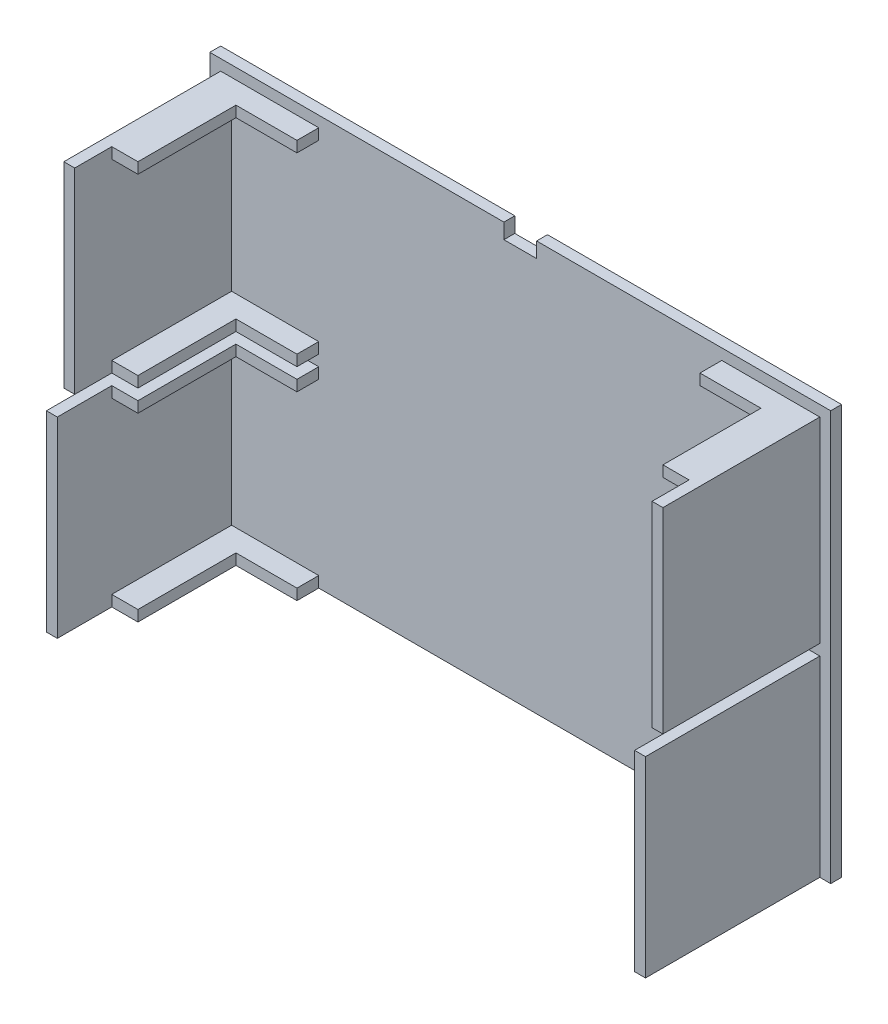
SolidWorks part; units mm, degrees
ref_plane "Front Plane" through (0, 0, 0) normal (0, 0, 1) x (1, 0, 0)
ref_plane "Top Plane" through (0, 0, 0) normal (0, 1, 0) x (1, 0, 0)
ref_plane "Right Plane" through (0, 0, 0) normal (1, 0, 0) x (0, 0, -1)
sketch "Sketch1" plane through (0, 0, 0) normal (0, 0, 1) x (1, 0, 0)
  line L1 (-138.7659, 75.117) -> (146.2341, 75.117)
  line L2 (-138.7659, 75.117) -> (-138.7659, -112.883)
  line L3 (-138.7659, -112.883) -> (146.2341, -112.883)
  line L4 (146.2341, 75.117) -> (146.2341, -112.883)
  dimension "D1" = 285
  dimension "D2" = 188
extrude "Boss-Extrude1" add sketch "Sketch1" along normal blind 5
sketch "Sketch2" plane through (0, -112.883, 0) normal (0, -1, 0) x (1, 0, 0)
  line L0 (-138.7659, 5) -> (146.2341, 5) construction
  line L1 (-3.7659, 5) -> (11.2341, 5)
  line L2 (-3.7659, 5) -> (-3.7659, 0)
  line L3 (-3.7659, 0) -> (11.2341, 0)
  line L4 (11.2341, 5) -> (11.2341, 0)
  line L5 (-138.7659, 0) -> (146.2341, 0) construction
  line L6 (-138.7659, 5) -> (-138.7659, 0) construction
  line L7 (146.2341, 5) -> (146.2341, 0) construction
  dimension "D1" = 15
  dimension "D2" = 135
  dimension "D3" = 135
sketch "Sketch3" plane through (0, 0, 5) normal (0, 0, 1) x (1, 0, 0)
  line L0 (146.2341, 75.117) -> (-138.7659, 75.117) construction
  line L1 (-133.7659, 70.117) -> (-128.7659, 70.117)
  line L2 (-133.7659, 70.117) -> (-133.7659, -19.883)
  line L3 (-133.7659, -19.883) -> (-128.7659, -19.883)
  line L4 (-128.7659, 70.117) -> (-128.7659, -19.883)
  line L5 (-138.7659, 75.117) -> (-138.7659, -112.883) construction
  dimension "D1" = 5
  dimension "D2" = 90
  dimension "D3" = 5
  dimension "D4" = 5
extrude "Boss-Extrude2" add sketch "Sketch3" along normal blind 72
sketch "Sketch6" plane through (0, 0, 5) normal (0, 0, 1) x (1, 0, 0)
  line L0 (-128.7659, 70.117) -> (-88.7659, 70.117)
  line L1 (-88.7659, 70.117) -> (-88.7659, 65.117)
  line L2 (-88.7659, 65.117) -> (-128.7659, 65.117)
  line L3 (-128.7659, -19.883) -> (-128.7659, 70.117) construction
  line L4 (-128.7659, 70.117) -> (-128.7659, 65.117)
  dimension "D1" = 40
  dimension "D2" = 5
  dimension "D3" = 40
extrude "Boss-Extrude3" add sketch "Sketch6" along normal blind 10
sketch "Sketch7" plane through (0, 0, 15) normal (0, 0, 1) x (1, 0, 0)
  line L0 (-128.7659, 70.117) -> (-116.7659, 70.117)
  line L1 (-88.7659, 70.117) -> (-133.7659, 70.117) construction
  line L2 (-116.7659, 70.117) -> (-116.7659, 65.117)
  line L3 (-128.7659, 65.117) -> (-88.7659, 65.117) construction
  line L4 (-116.7659, 65.117) -> (-128.7659, 65.117)
  line L5 (-128.7659, 65.117) -> (-88.7659, 65.117) construction
  line L6 (-128.7659, 65.117) -> (-128.7659, 70.117)
  dimension "D1" = 12
extrude "Boss-Extrude4" add sketch "Sketch7" along normal blind 45
sketch "Sketch8" plane through (0, 0, 77) normal (0, 0, 1) x (1, 0, 0)
  line L0 (-128.7659, -19.883) -> (-128.7659, 70.117) construction
  line L1 (-128.7659, -19.883) -> (-88.7659, -19.883)
  line L2 (-128.7659, -19.883) -> (-128.7659, -14.883)
  line L3 (-128.7659, -14.883) -> (-88.7659, -14.883)
  line L4 (-88.7659, -19.883) -> (-88.7659, -14.883)
  line L5 (-128.7659, -19.883) -> (-128.7659, 65.117) construction
  dimension "D1" = 5
  dimension "D2" = 40
extrude "Boss-Extrude5" add sketch "Sketch8" against normal blind 72
sketch "Sketch9" plane through (0, -19.883, 0) normal (0, -1, 0) x (1, 0, 0)
  line L0 (-116.7659, 15) -> (-88.7659, 15)
  line L1 (-88.7659, 5) -> (-88.7659, 77) construction
  line L2 (-88.7659, 15) -> (-88.7659, 77)
  line L3 (-88.7659, 77) -> (-128.7659, 77)
  line L4 (-128.7659, 77) -> (-128.7659, 60)
  line L5 (-128.7659, 60) -> (-116.7659, 60)
  line L6 (-116.7659, 60) -> (-116.7659, 15)
extrude "Cut-Extrude4" cut sketch "Sketch9" along normal through all both and the other way through all
sketch "Sketch11" plane through (0, 0, 5) normal (0, 0, 1) x (1, 0, 0)
  line L0 (3.7341, 75.117) -> (3.7341, -112.883) construction
  line L1 (146.2341, 75.117) -> (-138.7659, 75.117) construction
  line L2 (-138.7659, -112.883) -> (146.2341, -112.883) construction
sketch "Sketch13" plane through (0, 0, 5) normal (0, 0, 1) x (1, 0, 0)
  line L0 (146.2341, 75.117) -> (-138.7659, 75.117) construction
  line L1 (136.2341, 70.117) -> (141.2341, 70.117)
  line L2 (136.2341, 70.117) -> (136.2341, -19.883)
  line L3 (136.2341, -19.883) -> (141.2341, -19.883)
  line L4 (141.2341, 70.117) -> (141.2341, -19.883)
  line L5 (-128.7659, 70.117) -> (-133.7659, 70.117) construction
  line L8 (146.2341, -112.883) -> (146.2341, 75.117) construction
  dimension "D1" = 5
  dimension "D2" = 5
  dimension "D3" = 90
  dimension "D4" = 5
  dimension "D5" = 5
extrude "Boss-Extrude6" add sketch "Sketch13" along normal blind 72
sketch "Sketch14" plane through (0, 0, 5) normal (0, 0, 1) x (1, 0, 0)
  line L1 (136.2341, 70.117) -> (96.2341, 70.117)
  line L2 (136.2341, 70.117) -> (136.2341, 65.117)
  line L3 (136.2341, 65.117) -> (96.2341, 65.117)
  line L4 (96.2341, 70.117) -> (96.2341, 65.117)
  dimension "D1" = 40
  dimension "D2" = 5
extrude "Boss-Extrude7" add sketch "Sketch14" along normal blind 55
sketch "Sketch15" plane through (0, 65.117, 0) normal (0, -1, 0) x (1, 0, 0)
sketch "Sketch16" plane through (0, 65.117, 0) normal (0, -1, 0) x (1, 0, 0)
  line L1 (96.2341, 60) -> (124.2341, 60)
  line L2 (96.2341, 60) -> (96.2341, 15)
  line L3 (96.2341, 15) -> (124.2341, 15)
  line L4 (124.2341, 60) -> (124.2341, 15)
  dimension "D1" = 28
  dimension "D2" = 45
extrude "Cut-Extrude5" cut sketch "Sketch16" against normal through all both and the other way through all
sketch "Sketch17" plane through (0, 0, 0) normal (0, 0, 1) x (1, 0, 0)
  line L1 (136.2341, -19.883) -> (96.2341, -19.883)
  line L2 (136.2341, -19.883) -> (136.2341, -14.883)
  line L3 (136.2341, -14.883) -> (96.2341, -14.883)
  line L4 (96.2341, -19.883) -> (96.2341, -14.883)
  dimension "D1" = 40
  dimension "D2" = 5
extrude "Boss-Extrude9" add sketch "Sketch17" along normal blind 55
sketch "Sketch21" plane through (0, -14.883, 0) normal (0, 1, 0) x (1, 0, 0)
  line L0 (136.2341, -55) -> (96.2341, -55) construction
  line L1 (96.2341, -15) -> (123.996, -15)
  line L2 (96.2341, -15) -> (96.2341, -55)
  line L3 (96.2341, -55) -> (123.996, -55)
  line L4 (123.996, -15) -> (123.996, -55)
extrude "Cut-Extrude6" cut sketch "Sketch21" against normal through all both and the other way through all
sketch "Sketch22" plane through (0, 0, 5) normal (0, 0, 1) x (1, 0, 0)
  line L0 (-138.7659, -112.883) -> (146.2341, -112.883) construction
  line L1 (-133.7659, -24.883) -> (-128.7659, -24.883)
  line L2 (-133.7659, -24.883) -> (-133.7659, -112.883)
  line L3 (-133.7659, -112.883) -> (-128.7659, -112.883)
  line L4 (-128.7659, -24.883) -> (-128.7659, -112.883)
  line L6 (-133.7659, -19.883) -> (-128.7659, -19.883) construction
  line L7 (-138.7659, 75.117) -> (-138.7659, -112.883) construction
  line L8 (-133.7659, 70.117) -> (-133.7659, -19.883) construction
  dimension "D1" = 5
  dimension "D2" = 5
  dimension "D3" = 5
  dimension "D4" = 5
  dimension "D5" = 5
extrude "Boss-Extrude10" add sketch "Sketch22" along normal blind 80
sketch "Sketch23" plane through (0, 0, 5) normal (0, 0, 1) x (1, 0, 0)
  line L0 (-128.7659, -112.883) -> (-128.7659, -24.883) construction
  line L1 (-128.7659, -107.883) -> (-88.7659, -107.883)
  line L2 (-128.7659, -107.883) -> (-128.7659, -112.883)
  line L3 (-128.7659, -112.883) -> (-88.7659, -112.883)
  line L4 (-88.7659, -107.883) -> (-88.7659, -112.883)
  line L5 (-128.7659, -112.883) -> (146.2341, -112.883) construction
  dimension "D1" = 40
  dimension "D2" = 5
extrude "Boss-Extrude11" add sketch "Sketch23" along normal blind 55
sketch "Sketch25" plane through (0, -107.883, 0) normal (0, 1, 0) x (1, 0, 0)
  line L1 (-116.6577, -15.6268) -> (-88.7659, -15.6268)
  line L2 (-116.6577, -15.6268) -> (-116.6577, -60)
  line L3 (-116.6577, -60) -> (-88.7659, -60)
  line L4 (-88.7659, -15.6268) -> (-88.7659, -60)
extrude "Cut-Extrude7" cut sketch "Sketch25" against normal through all both and the other way through all
sketch "Sketch26" plane through (0, 0, 5) normal (0, 0, 1) x (1, 0, 0)
  line L1 (-128.7659, -24.883) -> (-88.7659, -24.883)
  line L2 (-128.7659, -24.883) -> (-128.7659, -29.883)
  line L3 (-128.7659, -29.883) -> (-88.7659, -29.883)
  line L4 (-88.7659, -24.883) -> (-88.7659, -29.883)
  dimension "D1" = 40
  dimension "D2" = 5
extrude "Boss-Extrude12" add sketch "Sketch26" along normal blind 55
sketch "Sketch27" plane through (0, -24.883, 0) normal (0, 1, 0) x (1, 0, 0)
  line L1 (-116.7659, -15) -> (-88.7659, -15)
  line L2 (-116.7659, -15) -> (-116.7659, -60)
  line L3 (-116.7659, -60) -> (-88.7659, -60)
  line L4 (-88.7659, -15) -> (-88.7659, -60)
extrude "Cut-Extrude9" cut sketch "Sketch27" against normal through all both and the other way through all
sketch "Sketch29" plane through (0, 0, 5) normal (0, 0, 1) x (1, 0, 0)
  line L0 (-88.7659, -112.883) -> (146.2341, -112.883) construction
  line L1 (141.2341, -112.883) -> (136.2341, -112.883)
  line L2 (141.2341, -112.883) -> (141.2341, -24.883)
  line L3 (141.2341, -24.883) -> (136.2341, -24.883)
  line L4 (136.2341, -112.883) -> (136.2341, -24.883)
  line L6 (146.2341, -112.883) -> (146.2341, 75.117) construction
  line L7 (136.2341, -19.883) -> (141.2341, -19.883) construction
  dimension "D1" = 5
  dimension "D2" = 5
  dimension "D3" = 5
  dimension "D4" = 5
  dimension "D5" = 88
extrude "Boss-Extrude14" add sketch "Sketch29" along normal blind 80
sketch "Sketch30" plane through (0, 0, 5) normal (0, 0, 1) x (1, 0, 0)
  line L2 (136.2341, -112.883) -> (96.2341, -112.883)
  line L3 (136.2341, -112.883) -> (136.2341, -107.883)
  line L4 (136.2341, -107.883) -> (96.2341, -107.883)
  line L5 (96.2341, -112.883) -> (96.2341, -107.883)
  dimension "D1" = 40
  dimension "D2" = 5
extrude "Boss-Extrude15" add sketch "Sketch30" along normal blind 55
sketch "Sketch31" plane through (0, -107.883, 0) normal (0, 1, 0) x (1, 0, 0)
  line L0 (136.2341, -60) -> (96.2341, -60) construction
  line L1 (96.2341, -15) -> (124.0806, -15)
  line L2 (96.2341, -15) -> (96.2341, -60)
  line L3 (96.2341, -60) -> (124.0806, -60)
  line L4 (124.0806, -15) -> (124.0806, -60)
extrude "Cut-Extrude10" cut sketch "Sketch31" against normal through all both and the other way through all
sketch "Sketch32" plane through (0, 0, 5) normal (0, 0, 1) x (1, 0, 0)
  line L1 (136.2341, -24.883) -> (96.2341, -24.883)
  line L2 (136.2341, -24.883) -> (136.2341, -29.883)
  line L3 (136.2341, -29.883) -> (96.2341, -29.883)
  line L4 (96.2341, -24.883) -> (96.2341, -29.883)
  dimension "D1" = 40
  dimension "D2" = 5
extrude "Boss-Extrude16" add sketch "Sketch32" along normal blind 55
sketch "Sketch33" plane through (0, -29.883, 0) normal (0, -1, 0) x (1, 0, 0)
  line L1 (96.2341, 60) -> (124.0806, 60)
  line L2 (96.2341, 60) -> (96.2341, 15)
  line L3 (96.2341, 15) -> (124.0806, 15)
  line L4 (124.0806, 60) -> (124.0806, 15)
extrude "Cut-Extrude11" cut sketch "Sketch33" against normal through all both and the other way through all
sketch "Sketch36" plane through (0, 75.117, 0) normal (0, 1, 0) x (1, 0, 0)
  line L0 (146.2341, 0) -> (-138.7659, 0) construction
  line L1 (-3.7659, 0) -> (11.2341, 0)
  line L2 (-3.7659, 0) -> (-3.7659, -5)
  line L3 (-3.7659, -5) -> (11.2341, -5)
  line L4 (11.2341, 0) -> (11.2341, -5)
  line L5 (146.2341, -5) -> (-138.7659, -5) construction
  line L6 (-138.7659, -5) -> (-138.7659, 0) construction
  line L7 (146.2341, -5) -> (146.2341, 0) construction
  point P10 (11.2341, -2.5)
  dimension "D1" = 135
  dimension "D2" = 135
extrude "Cut-Extrude12" cut sketch "Sketch36" against normal blind 7 and the other way through all
